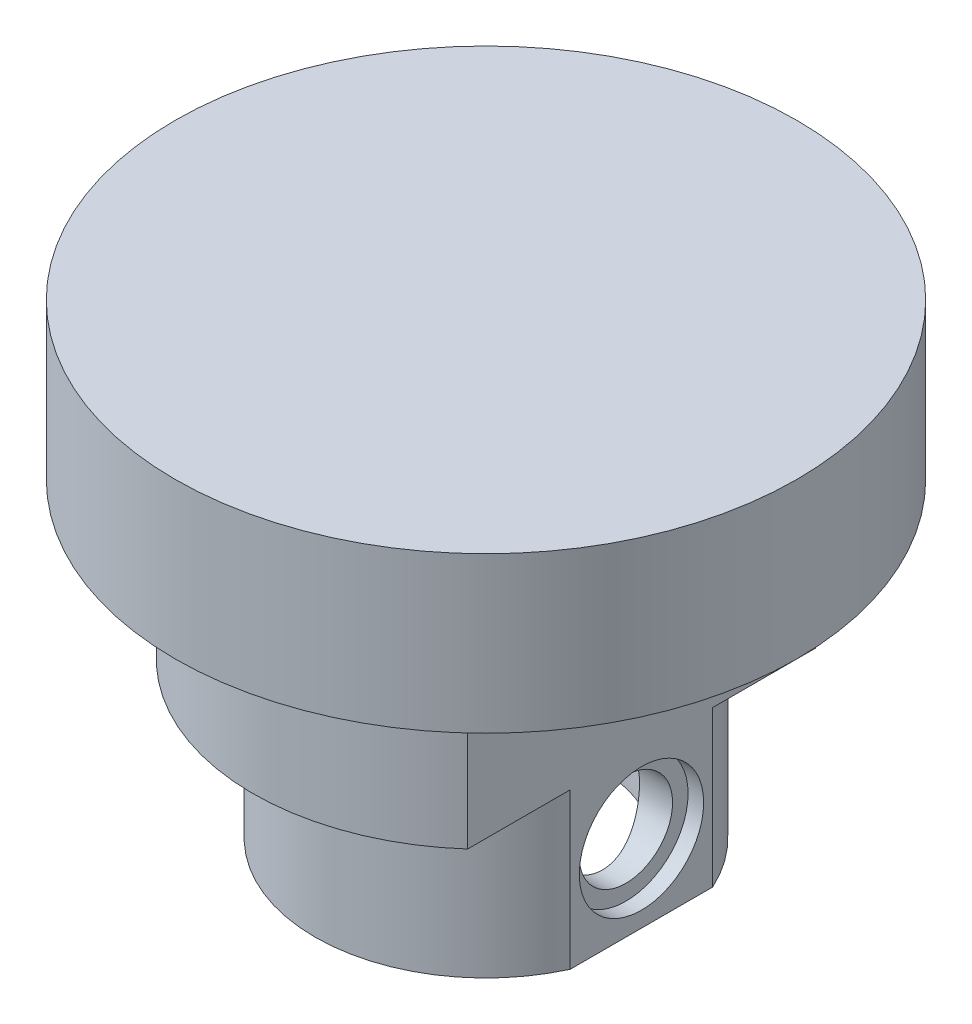
SolidWorks part; units mm, degrees
material "3003 Alloy"
ref_plane "Front Plane" through (0, 0, 0) normal (0, 0, 1) x (1, 0, 0)
ref_plane "Top Plane" through (0, 0, 0) normal (0, 1, 0) x (1, 0, 0)
ref_plane "Right Plane" through (0, 0, 0) normal (1, 0, 0) x (0, 0, -1)
sketch "Sketch1" plane through (0, 0, 0) normal (0, 1, 0) x (1, 0, 0)
  circle A0 centre (0, 0) radius 20
  dimension "D1" = 40
extrude "Stock" add sketch "Sketch1" against normal blind 20
sketch "Sketch2" plane through (0, 0, 0) normal (0, 1, 0) x (1, 0, 0)
  circle A0 centre (0, 0) radius 15
  dimension "D1" = 30
extrude "Cut-Extrude1" cut sketch "Sketch2" against normal up to surface (10 mm away) from offset 10 flip side to cut up to face at (0, -20, 20) offset against normal yes
sketch "Sketch4" plane through (0, 0, 0) normal (0, 1, 0) x (1, 0, 0)
  circle A0 centre (0, 0) radius 11
  dimension "D1" = 22
extrude "Boss-Extrude2" add sketch "Sketch4" against normal blind 10 from surface at -20 starting at face at (0, -20, 15)
sketch "Sketch3" plane through (0, 0, 0) normal (0, 1, 0) x (1, 0, 0)
  line L0 (10, -11.1803) -> (10, 11.1803)
  circle A0 centre (0, 0) radius 15 construction
  dimension "D1" = 10
extrude "MainKey" cut sketch "Sketch3" against normal through all from surface thin
sketch "Sketch5" plane through (0, 0, 0) normal (0, 1, 0) x (1, 0, 0)
  circle A0 centre (0, 0) radius 7.5
  dimension "D1" = 15
extrude "CentreBore" cut sketch "Sketch5" along normal offset from surface (25 mm away) 5 from surface at -30 up to face at (0, 0, 20) starting at face at (-0.5, -30, 0)
sketch "Sketch6" plane through (10, 0, 0) normal (1, 0, 0) x (0, 0, -1)
  line L0 (-11.1803, -10) -> (11.1803, -10) construction
  circle A0 centre (0, -25) radius 3
  dimension "D1" = 6
  dimension "D2" = 15
extrude "Holes" cut sketch "Sketch6" against normal offset from surface (23.6748 mm away) 1
sketch "Sketch7" plane through (10, 0, 0) normal (1, 0, 0) x (0, 0, -1)
  circle A0 centre (0, -25) radius 4
  dimension "D1" = 8
extrude "Cut-Extrude4" cut sketch "Sketch7" against normal blind 1
